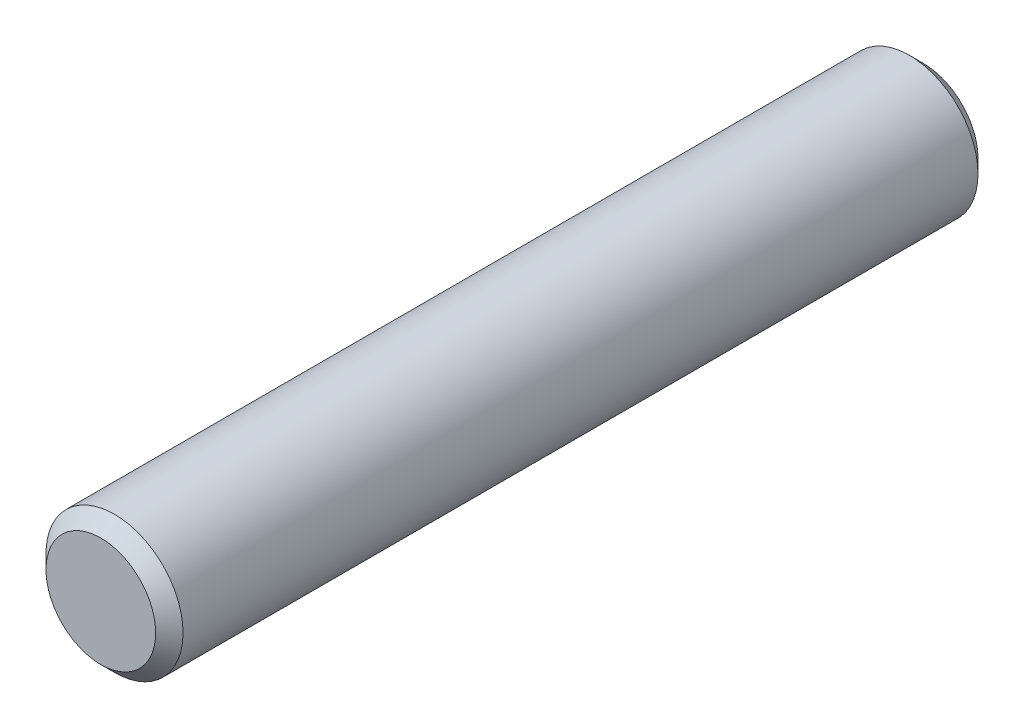
SolidWorks part; units mm, degrees
material "1.4310 (X10CrNi18-8)"
ref_plane "Front Plane" through (0, 0, 0) normal (0, 0, 1) x (1, 0, 0)
ref_plane "Top Plane" through (0, 0, 0) normal (0, 1, 0) x (1, 0, 0)
ref_plane "Right Plane" through (0, 0, 0) normal (1, 0, 0) x (0, 0, -1)
sketch "Sketch1" plane through (0, 0, 0) normal (0, 0, 1) x (1, 0, 0)
  circle A0 centre (0, 0) radius 2.5
  dimension "D1" = 5
extrude "Boss-Extrude1" add sketch "Sketch1" along normal mid plane 30
chamfer "Chamfer1" distance 0.5 angle 45 2 edges at (2.5, 0, -15) (2.5, 0, 15)
